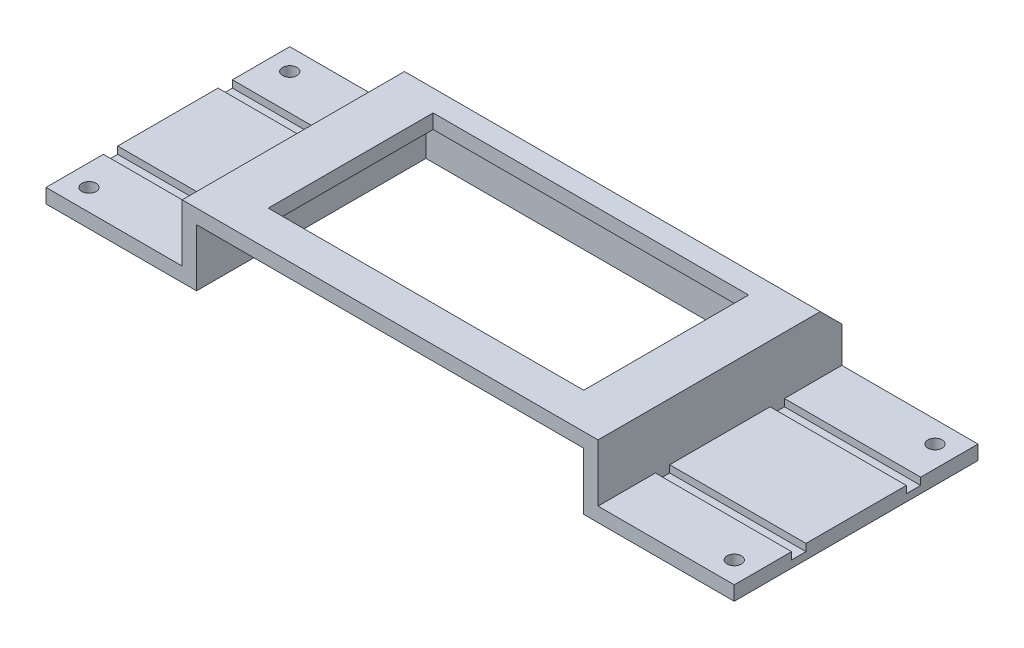
SolidWorks part; units mm, degrees
ref_plane "Front" through (0, 0, 0) normal (0, 0, 1) x (1, 0, 0)
ref_plane "Top" through (0, 0, 0) normal (0, 1, 0) x (1, 0, 0)
ref_plane "Right" through (0, 0, 0) normal (1, 0, 0) x (0, 0, -1)
sketch "草图1" plane through (0, 0, 0) normal (0, 1, 0) x (1, 0, 0)
  line L1 (24, -8.5) -> (-24, -8.5)
  line L2 (24, -8.5) -> (24, 8.5)
  line L3 (24, 8.5) -> (-24, 8.5)
  line L4 (-24, -8.5) -> (-24, 8.5)
  line L5 (24, -8.5) -> (-24, 8.5) construction
  line L6 (24, 8.5) -> (-24, -8.5) construction
  point P0 (0, 0)
  dimension "D1" = 48
  dimension "D2" = 17
extrude "凸台-拉伸1" add sketch "草图1" along normal blind 1
sketch "草图2" plane through (0, 1, 0) normal (0, 1, 0) x (1, 0, 0)
  line L0 (24, 8.5) -> (-24, 8.5) construction
  line L1 (14.5, -8.5) -> (-14.5, -8.5)
  line L2 (14.5, -8.5) -> (14.5, 8.5)
  line L3 (14.5, 8.5) -> (-14.5, 8.5)
  line L4 (-14.5, -8.5) -> (-14.5, 8.5)
  line L5 (14.5, -8.5) -> (-14.5, 8.5) construction
  line L6 (14.5, 8.5) -> (-14.5, -8.5) construction
  point P0 (0, 0)
  dimension "D1" = 29
extrude "凸台-拉伸2" add sketch "草图2" along normal blind 4
sketch "草图3" plane through (0, 0, 0) normal (0, -1, 0) x (1, 0, 0)
  line L0 (0, -2.3899) -> (0, 23.5479) construction
  line L1 (13.5, -7.5) -> (-13.5, -7.5)
  line L2 (13.5, -7.5) -> (13.5, 8.5)
  line L3 (13.5, 8.5) -> (-13.5, 8.5)
  line L4 (-13.5, -7.5) -> (-13.5, 8.5)
  line L5 (13.5, -7.5) -> (-13.5, 8.5) construction
  line L6 (13.5, 8.5) -> (-13.5, -7.5) construction
  line L7 (-24, 8.5) -> (24, 8.5) construction
  line L8 (14.5, -8.5) -> (-14.5, -8.5) construction
  point P0 (0, 0)
  point P6 (0, 0.5)
  dimension "D1" = 27
  dimension "D2" = 1
extrude "切除-拉伸1" cut sketch "草图3" against normal offset from surface (4 mm away) 1 up to face at (0, 5, 0)
sketch "草图4" plane through (0, 5, 0) normal (0, 1, 0) x (1, 0, 0)
  line L0 (0, 19.0744) -> (0, -13.1594) construction
  line L1 (14.5, 8.5) -> (-14.5, 8.5) construction
  line L2 (11, -6) -> (-11, -6)
  line L3 (11, -6) -> (11, 5.5)
  line L4 (11, 5.5) -> (-11, 5.5)
  line L5 (-11, -6) -> (-11, 5.5)
  line L6 (11, -6) -> (-11, 5.5) construction
  line L7 (11, 5.5) -> (-11, -6) construction
  point P3 (0, -0.25)
  dimension "D1" = 11.5
  dimension "D2" = 22
  dimension "D3" = 3
extrude "切除-拉伸2" cut sketch "草图4" against normal through all
chamfer "倒角1" distance 1.5 angle 45 1 edges at (0, 5, -8.5)
sketch "草图5" plane through (0, 1, 0) normal (0, 1, 0) x (1, 0, 0)
  line L2 (-5.1676, 0) -> (10.3225, 0) construction
  line L3 (0, 22.2952) -> (0, -13.684) construction
  circle A0 centre (-22.5, 7) radius 0.5
  circle A1 centre (22.5, 7) radius 0.5
  circle A2 centre (22.5, -7) radius 0.5
  circle A3 centre (-22.5, -7) radius 0.5
  dimension "D1" = 1
  dimension "D2" = 45
  dimension "D4" = 14
extrude "切除-拉伸3" cut sketch "草图5" against normal through all
sketch "草图6" plane through (0, 1, 0) normal (0, 1, 0) x (1, 0, 0)
  line L0 (0, 16.9384) -> (0, -11.0888) construction
  line L1 (-24, 8.5) -> (-24, -8.5) construction
  line L2 (-14.5, 3.5) -> (-24, 3.5)
  line L3 (-14.5, 3.5) -> (-14.5, 4.5)
  line L4 (-14.5, 4.5) -> (-24, 4.5)
  line L5 (-24, 3.5) -> (-24, 4.5)
  line L6 (-14.5, 3.5) -> (-24, 4.5) construction
  line L7 (-14.5, 4.5) -> (-24, 3.5) construction
  line L8 (-14.5, 8.5) -> (-14.5, -8.5) construction
  line L13 (-30.2518, 0) -> (32.7674, 0) construction
  line L14 (-14.5, -4.5) -> (-24, -3.5) construction
  line L15 (-14.5, -3.5) -> (-24, -4.5) construction
  line L16 (-24, -3.5) -> (-24, -4.5)
  line L17 (-14.5, -4.5) -> (-24, -4.5)
  line L18 (-14.5, -3.5) -> (-14.5, -4.5)
  line L19 (-14.5, -3.5) -> (-24, -3.5)
  line L20 (14.5, -3.5) -> (24, -4.5) construction
  line L21 (14.5, -4.5) -> (24, -3.5) construction
  line L22 (14.5, 4.5) -> (24, 3.5) construction
  line L23 (14.5, 3.5) -> (24, 4.5) construction
  line L24 (14.5, -3.5) -> (24, -3.5)
  line L25 (14.5, -3.5) -> (14.5, -4.5)
  line L26 (14.5, -4.5) -> (24, -4.5)
  line L27 (24, -3.5) -> (24, -4.5)
  line L28 (24, 3.5) -> (24, 4.5)
  line L29 (14.5, 4.5) -> (24, 4.5)
  line L30 (14.5, 3.5) -> (14.5, 4.5)
  line L31 (14.5, 3.5) -> (24, 3.5)
  point P3 (-19.25, 4)
  point P18 (-19.25, -4)
  point P27 (19.25, -4)
  point P28 (19.25, 4)
  dimension "D1" = 1
  dimension "D2" = 8
extrude "切除-拉伸4" cut sketch "草图6" against normal blind 0.5
